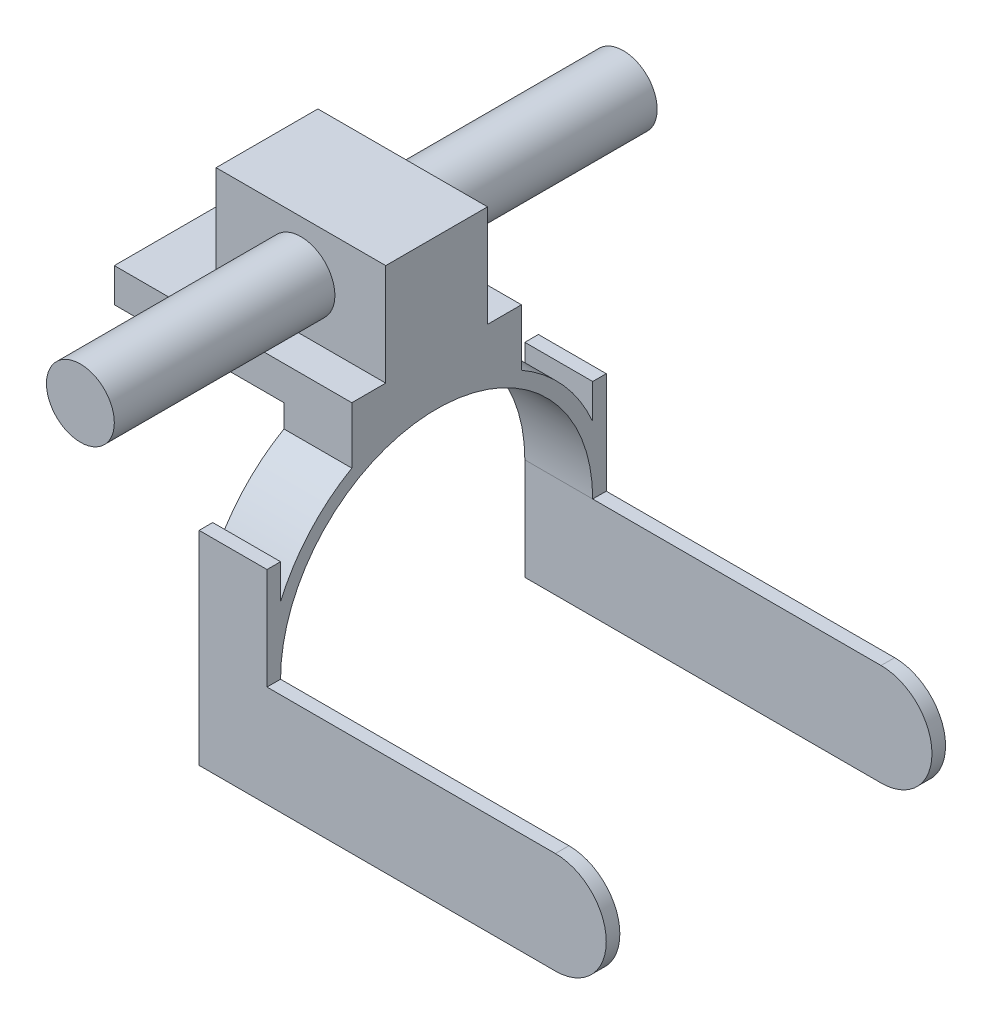
SolidWorks part; units mm, degrees
ref_plane "Front" through (0, 0, 0) normal (0, 0, 1) x (1, 0, 0)
ref_plane "Top" through (0, 0, 0) normal (0, 1, 0) x (1, 0, 0)
ref_plane "Right" through (0, 0, 0) normal (1, 0, 0) x (0, 0, -1)
sketch "草图1" plane through (0, 0, 0) normal (1, 0, 0) x (0, 0, -1)
  line L0 (0, 0) -> (-50.8301, 0) construction
  line L1 (-25, 5) -> (25, 5)
  line L2 (-25, 5) -> (-25, -5)
  line L4 (25, 5) -> (25, -5)
  line L5 (0, 0) -> (0, 38.695) construction
  line L6 (0, -5) -> (0, -75.8031) construction
  line L7 (-25, -5) -> (-25, -11.6988)
  line L8 (25, -5) -> (25, -11.6988)
  line L10 (-46, -55.0831) -> (-46, -85.0831)
  line L11 (-50, -25.0831) -> (-46, -25.0831)
  line L12 (-50, -25.0831) -> (-50, -85.0831)
  line L13 (-50, -85.0831) -> (-46, -85.0831)
  line L14 (-46, -25.0831) -> (-46, -35.3044)
  line L15 (46, -25.0831) -> (50, -25.0831)
  line L16 (46, -25.0831) -> (46, -35.3044)
  line L17 (46, -85.0831) -> (50, -85.0831)
  line L18 (50, -25.0831) -> (50, -85.0831)
  line L20 (46, -55.0831) -> (46, -85.0831)
  arc A1 (46, -55.0831) -> (-46, -55.0831) centre (0, -55.0831) ccw
  arc A3 (46, -35.3044) -> (25, -11.6988) centre (0, -55.0831) ccw
  arc A4 (-25, -11.6988) -> (-46, -35.3044) centre (0, -55.0831) ccw
  dimension "D5" = 60
  dimension "D1" = 50
  dimension "D2" = 25
  dimension "D3" = 10
  dimension "D8" = 50
  dimension "D9" = 50
  dimension "D10" = 4
  dimension "D11" = 60
extrude "凸台-拉伸1" add sketch "草图1" along normal blind 20
sketch "草图2" plane through (20, 0, 0) normal (1, 0, 0) x (0, 0, -1)
  line L0 (50, -85.0831) -> (50, -25.0831) construction
  line L1 (-50, -85.0831) -> (-46, -85.0831)
  line L2 (-50, -85.0831) -> (-50, -55.0831)
  line L3 (-50, -55.0831) -> (-46, -55.0831)
  line L4 (-46, -85.0831) -> (-46, -55.0831)
  line L5 (46, -85.0831) -> (50, -85.0831)
  line L6 (46, -85.0831) -> (46, -55.0831)
  line L7 (46, -55.0831) -> (50, -55.0831)
  line L8 (50, -85.0831) -> (50, -55.0831)
extrude "凸台-拉伸2" add sketch "草图2" along normal blind 100
sketch "草图3" plane through (0, 0, 50) normal (0, 0, 1) x (1, 0, 0)
  line L0 (120, -70.0831) -> (0, -70.0831) construction
  line L1 (120, -55.0831) -> (120, -85.0831) construction
  line L2 (0, -25.0831) -> (0, -85.0831) construction
  line L3 (120, -55.0831) -> (120, -85.0831) construction
  line L4 (105, -55.0831) -> (132.3601, -55.0831)
  line L5 (132.3601, -55.0831) -> (132.3601, -85.0831)
  line L6 (132.3601, -85.0831) -> (105, -85.0831)
  arc A0 (105, -85.0831) -> (105, -55.0831) centre (105, -70.0831) ccw
  dimension "D1" = 15
extrude "切除-拉伸1" cut sketch "草图3" against normal blind 100
sketch "草图4" plane through (0, 0, 0) normal (-1, 0, 0) x (0, 0, 1)
  line L0 (25, 5) -> (25, -11.6988) construction
  line L1 (-25, 5) -> (25, 5)
  line L2 (-25, 5) -> (-25, -5)
  line L3 (-25, -5) -> (25, -5)
  line L4 (25, 5) -> (25, -5)
  dimension "D1" = 10
extrude "凸台-拉伸3" add sketch "草图4" along normal blind 50
sketch "草图5" plane through (0, 5, 0) normal (0, 1, 0) x (1, 0, 0)
  line L0 (20, 25) -> (20, -25) construction
  line L1 (20, 15) -> (-30, 15)
  line L2 (20, 15) -> (20, -15)
  line L3 (20, -15) -> (-30, -15)
  line L4 (-30, 15) -> (-30, -15)
  dimension "D1" = 30
  dimension "D2" = 15
  dimension "D3" = 50
extrude "凸台-拉伸4" add sketch "草图5" along normal blind 30
sketch "草图6" plane through (0, 0, 0) normal (0, 0, 1) x (1, 0, 0)
  line L0 (-30, 19.7836) -> (20, 20) construction
  line L1 (-30, 35) -> (-30, 5) construction
  line L2 (20, 35) -> (20, 5) construction
  circle A0 centre (-5, 19.8918) radius 10
extrude "凸台-拉伸5" add sketch "草图6" along normal mid plane 160
